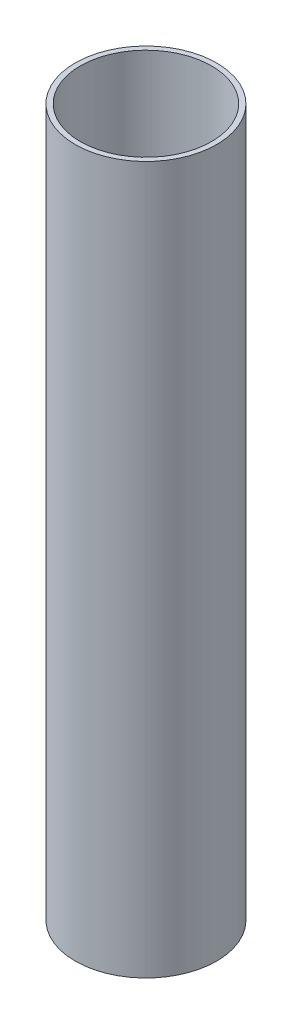
SolidWorks part; units mm, degrees
material "PVC 0.007 Plasticized"
ref_plane "Front Plane" through (0, 0, 0) normal (0, 0, 1) x (1, 0, 0)
ref_plane "Top Plane" through (0, 0, 0) normal (0, 1, 0) x (1, 0, 0)
ref_plane "Right Plane" through (0, 0, 0) normal (1, 0, 0) x (0, 0, -1)
sketch "Sketch1" plane through (0, 0, 0) normal (0, 1, 0) x (1, 0, 0)
  circle A0 centre (0, 0) radius 25
  circle A1 centre (0, 0) radius 23.2
  dimension "D1" = 50
  dimension "D2" = 46.4
extrude "Boss-Extrude1" add sketch "Sketch1" along normal mid plane 250
